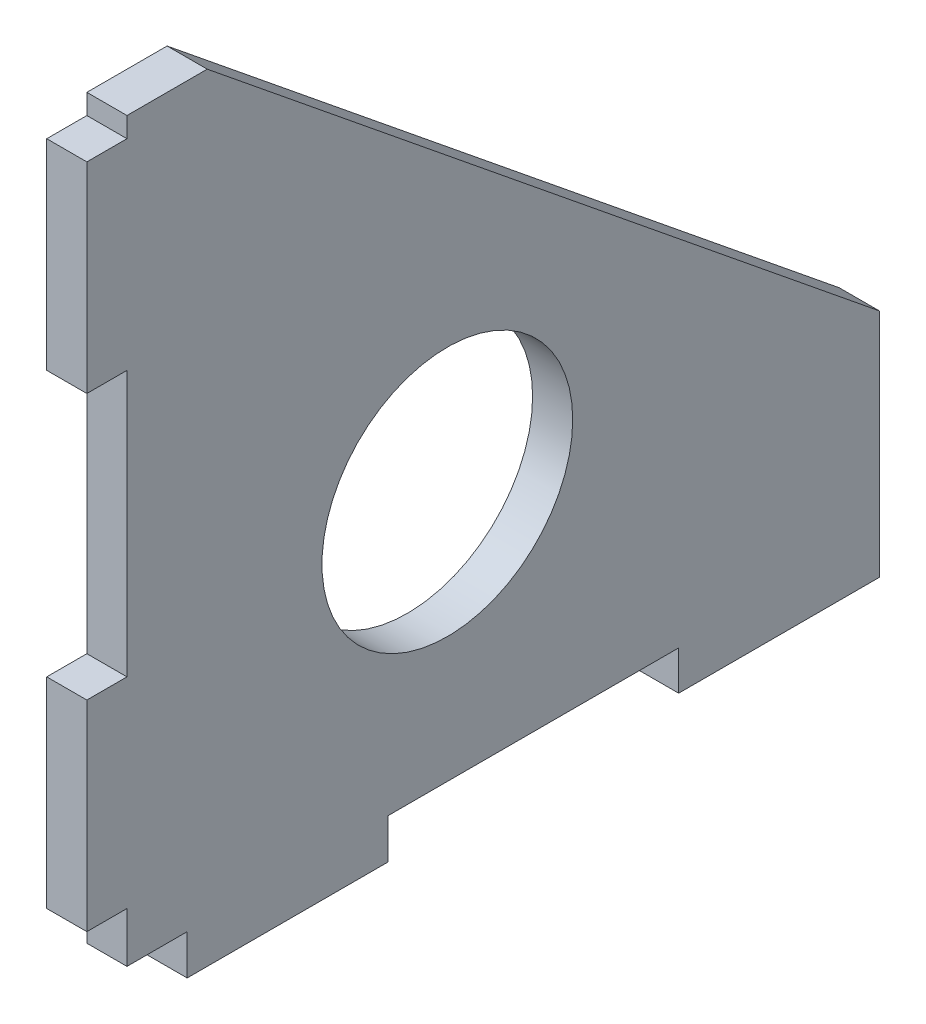
SolidWorks part; units mm, degrees
ref_plane "Front Plane" through (0, 0, 0) normal (0, 0, 1) x (1, 0, 0)
ref_plane "Top Plane" through (0, 0, 0) normal (0, 1, 0) x (1, 0, 0)
ref_plane "Right Plane" through (0, 0, 0) normal (1, 0, 0) x (0, 0, -1)
sketch "Sketch1" plane through (0, 0, 0) normal (1, 0, 0) x (0, 0, -1)
  line L0 (-32.1451, 34.053) -> (-32.1451, 14.053)
  line L1 (-32.1451, 14.053) -> (-28.1451, 14.053)
  line L2 (-28.1451, 14.053) -> (-28.1451, -12.4098)
  line L3 (-28.1451, -12.4098) -> (-32.1451, -12.4098)
  line L4 (-32.1451, -12.4098) -> (-32.1451, -32.4098)
  line L5 (-32.1451, -32.4098) -> (-28.1451, -32.4098)
  line L6 (-28.1451, -32.4098) -> (-28.1451, -37.4098)
  line L7 (-28.1451, -37.4098) -> (-22.1451, -37.4098)
  line L8 (-22.1451, -37.4098) -> (-22.1451, -41.4098)
  line L9 (-22.1451, -41.4098) -> (-2.1451, -41.4098)
  line L10 (-2.1451, -41.4098) -> (-2.1451, -37.4098)
  line L11 (-2.1451, -37.4098) -> (26.8549, -37.4098)
  line L12 (26.8549, -37.4098) -> (26.8549, -41.3227)
  line L13 (26.8549, -41.3227) -> (46.8549, -41.3227)
  line L15 (46.8549, -41.3227) -> (46.8549, -18.3086)
  line L16 (46.8549, -18.3086) -> (-20.1451, 36.057)
  line L18 (-28.1451, 36.057) -> (-28.1451, 34.053)
  line L19 (-32.1451, 34.053) -> (-28.1451, 34.053)
  line L20 (-28.1451, 36.057) -> (-20.1451, 36.057)
  circle A0 centre (3.7938, -12.4098) radius 12.5
  point P18 (-30.1451, 34.053)
  dimension "D17" = 25
  dimension "D1" = 20
  dimension "D2" = 26.4627
  dimension "D3" = 20
  dimension "D4" = 8
  dimension "D5" = 2.0041
  dimension "D6" = 5
  dimension "D7" = 4
  dimension "D8" = 4
  dimension "D9" = 20
  dimension "D10" = 29
  dimension "D11" = 20
  dimension "D12" = 4
  dimension "D13" = 6
  dimension "D14" = 4
  dimension "D15" = 4
  dimension "D16" = 4
extrude "Boss-Extrude1" add sketch "Sketch1" along normal blind 4
